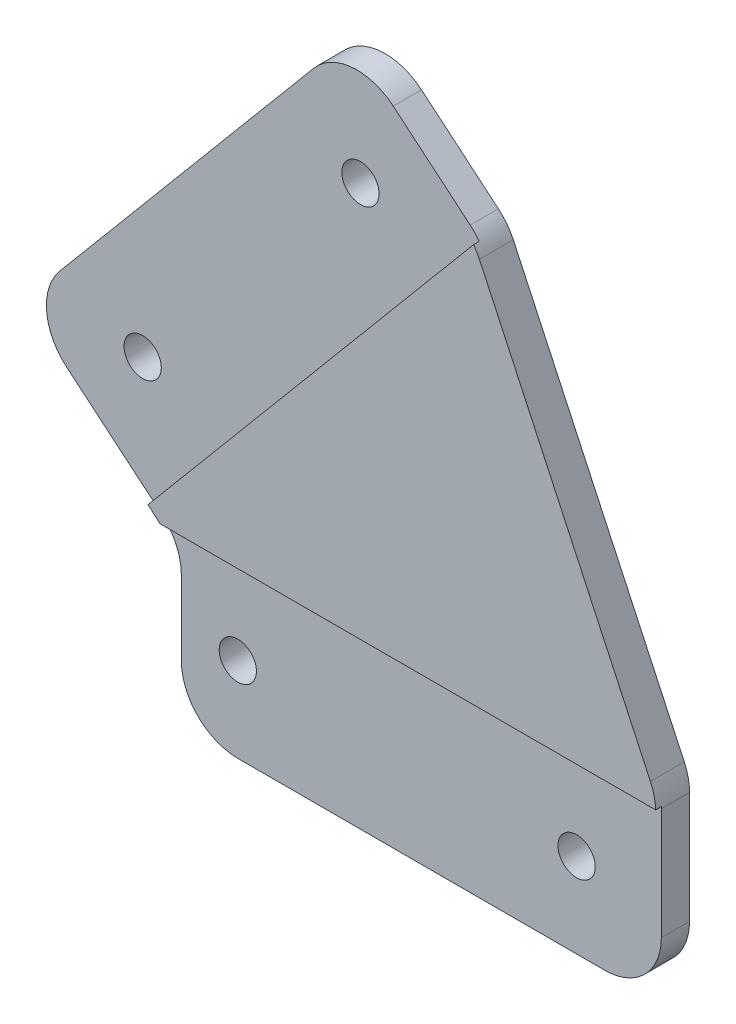
SolidWorks part; units mm, degrees
material "3.1325 (EN-AW 2017A)"
ref_plane "正面" through (0, 0, 0) normal (0, 0, 1) x (1, 0, 0)
ref_plane "平面" through (0, 0, 0) normal (0, 1, 0) x (1, 0, 0)
ref_plane "右側面" through (0, 0, 0) normal (1, 0, 0) x (0, 0, -1)
sketch "ｽｹｯﾁ1" plane through (0, 0, 0) normal (0, 0, 1) x (1, 0, 0)
  line L0 (0, 0) -> (306.8848, 365.731) construction
  line L1 (306.8848, 365.731) -> (440, 0) construction
  line L2 (440, 0) -> (0, 0) construction
  line L3 (306.8848, 365.731) -> (306.8848, 0) construction
  line L4 (306.8848, 365.731) -> (0, 0) construction
  line L9 (306.8848, 365.731) -> (295.3941, 375.3729)
  line L13 (0, 0) -> (0, -16)
  line L14 (0, -16) -> (45, -16)
  line L15 (45, -16) -> (45, 0)
  line L16 (45, 0) -> (28.9254, 34.472)
  line L17 (28.9254, 34.472) -> (17.4348, 44.1138)
  line L18 (17.4348, 44.1138) -> (-11.4907, 9.6418)
  line L19 (-11.4907, 9.6418) -> (0, 0)
  line L20 (0, 0) -> (2.5, -2.0977)
  line L21 (2.5, -2.0977) -> (2.5, -16)
  dimension "D4" = 16
  dimension "D5" = 15
  dimension "D6" = 45
  dimension "D1" = 440
  dimension "D2" = 70
  dimension "D3" = 50
  dimension "D7" = 45
  dimension "D8" = 2.5
extrude "ﾎﾞｽ - 押し出し1" add sketch "ｽｹｯﾁ1" along normal blind 3 contours L18 L19 L13 L14 L15 L16 L17
sketch "ｽｹｯﾁ2" plane through (0, 0, 3) normal (0, 0, 1) x (1, 0, 0)
  line L1 (45, -16) -> (45, 0) construction
  line L2 (2.5, -16) -> (45, -16) construction
  line L3 (-11.4907, 9.6418) -> (2.5, -2.0977) construction
  line L4 (17.4348, 44.1138) -> (-11.4907, 9.6418) construction
  line L5 (28.9254, 34.472) -> (17.4348, 44.1138) construction
  circle A0 centre (7.5, -8.5) radius 1.65
  circle A1 centre (-0.9244, 10.5662) radius 1.65
  circle A2 centre (18.3592, 33.5476) radius 1.65
  circle A3 centre (37.5, -8.5) radius 1.65
  dimension "D2" = 7.5
  dimension "D3" = 7.5
  dimension "D4" = 7.5
  dimension "D5" = 3.3
  dimension "D6" = 3.3
  dimension "D7" = 3.3
  dimension "D8" = 3.3
  dimension "D9" = 7.5
  dimension "D10" = 7.5
  dimension "D11" = 7.5
  dimension "D12" = 7.5
  dimension "D13" = 30
extrude "ｶｯﾄ - 押し出し1" cut sketch "ｽｹｯﾁ2" against normal blind 3
fillet "ﾌｨﾚｯﾄ2" radius 5 7 edges at (28.9254, 34.472, 1.5) (45, 0, 1.5) (45, -16, 1.5) (-11.4907, 9.6418, 1.5) (17.4348, 44.1138, 1.5) (2.5, -16, 1.5) (2.5, -2.0977, 1.5)
sketch "ｽｹｯﾁ3" plane through (0, 0, 3) normal (0, 0, 1) x (1, 0, 0)
  line L0 (17.4348, 44.1138) -> (-12.1335, 8.8758)
  line L1 (17.4348, 44.1138) -> (28.9637, 34.4399)
  line L2 (-12.1335, 8.8758) -> (-0.6045, -0.7982)
  line L3 (28.9637, 34.4399) -> (-0.6045, -0.7982)
  line L4 (14.2208, 40.2836) -> (-8.2767, 13.472) construction
  line L5 (0.5, -16) -> (45, -16)
  line L6 (0.5, -16) -> (0.5, -0.95)
  line L7 (45, -16) -> (45, -0.95)
  line L8 (0.5, -0.95) -> (45, -0.95)
  line L9 (7.5, -16) -> (40, -16) construction
  line L10 (28.0763, 35.1845) -> (21.265, 40.8999) construction
  line L11 (45, -11) -> (45, -1.1085) construction
  line L12 (-7.6604, 6.4279) -> (0.7139, -0.5991) construction
  line L13 (2.5, -4.4293) -> (2.5, -11) construction
  dimension "D1" = 15.05
  dimension "D2" = 15.05
  dimension "D3" = 1
  dimension "D4" = 2
extrude "ｶｯﾄ - 押し出し2" cut sketch "ｽｹｯﾁ3" against normal blind 0.5
